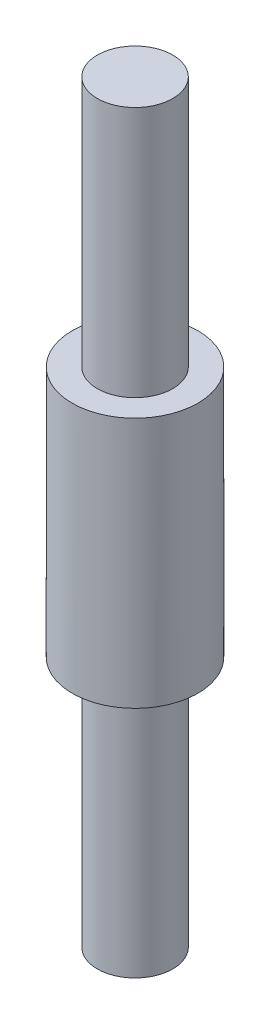
SolidWorks part; units mm, degrees
ref_plane "Front Plane" through (0, 0, 0) normal (0, 0, 1) x (1, 0, 0)
ref_plane "Top Plane" through (0, 0, 0) normal (0, 1, 0) x (1, 0, 0)
ref_plane "Right Plane" through (0, 0, 0) normal (1, 0, 0) x (0, 0, -1)
sketch "Sketch1" plane through (0, 0, 0) normal (0, 1, 0) x (1, 0, 0)
  circle A0 centre (0, 0) radius 2.5
  dimension "D1" = 5
extrude "Boss-Extrude1" add sketch "Sketch1" along normal mid plane 30
sketch "Sketch2" plane through (0, 15, 0) normal (0, 1, 0) x (1, 0, 0)
  circle A2 centre (0, 0) radius 12.5
  circle A3 centre (0, 0) radius 12.5
  circle A5 centre (0, 0) radius 1.5
  circle A6 centre (0, 0) radius 1.5
  dimension "D1" = 10
  dimension "D2" = 1
extrude "Cut-Extrude1" cut sketch "Sketch2" against normal blind 10
mirror "Mirror1" about plane through (0, 0, 0) normal (0, 1, 0) of "Cut-Extrude1"
